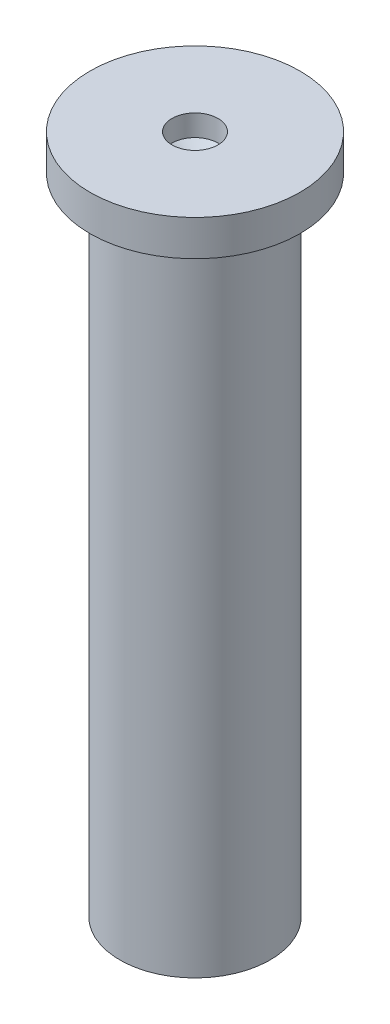
SolidWorks part; units mm, degrees
ref_plane "Front Plane" through (0, 0, 0) normal (0, 0, 1) x (1, 0, 0)
ref_plane "Top Plane" through (0, 0, 0) normal (0, 1, 0) x (1, 0, 0)
ref_plane "Right Plane" through (0, 0, 0) normal (1, 0, 0) x (0, 0, -1)
sketch "Sketch1" plane through (0, 0, 0) normal (0, 0, 1) x (1, 0, 0)
  line L0 (0, 0) -> (0, 8.7656) construction
  line L1 (0, 0) -> (1.05, 0)
  line L2 (1.05, 0) -> (1.05, 9)
  line L3 (1.05, 9) -> (1.4682, 9)
  line L4 (1.4682, 9) -> (1.4682, 9.5)
  line L5 (1.4682, 9.5) -> (0.3212, 9.5)
  line L6 (0.3212, 9.5) -> (0.3212, 9.2015)
  line L7 (0.3212, 9.2015) -> (0, 9)
  line L8 (0, 0) -> (0, 9)
  point P4 (0.4803, 6.1271)
  point P11 (0, 6)
  point P12 (0.3212, 6.2015)
  point P13 (0, 0)
  dimension "D1" = 2.1
  dimension "D2" = 9
  dimension "D3" = 0.5
revolve "Revolve1" add sketch "Sketch1" angle 360 about L0
